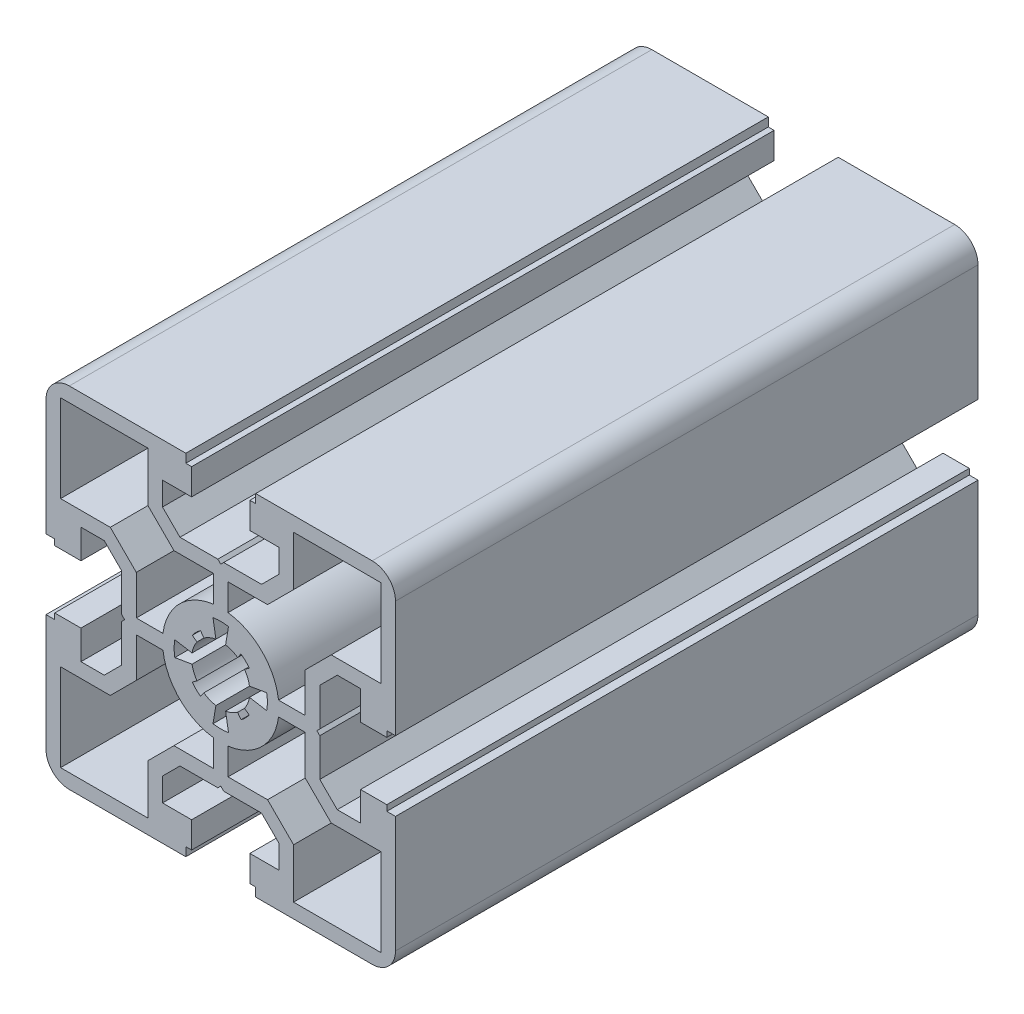
SolidWorks part; units mm, degrees
ref_plane "Ön Düzlem" through (0, 0, 0) normal (0, 0, 1) x (1, 0, 0)
ref_plane "Üst Düzlem" through (0, 0, 0) normal (0, 1, 0) x (1, 0, 0)
ref_plane "Sağ Düzlem" through (0, 0, 0) normal (1, 0, 0) x (0, 0, -1)
ref_plane "Düzlem1" through (0, 0, 100) normal (0, 0, 1) x (1, 0, 0)
sketch "Çizim1" plane through (0, 0, 100) normal (0, 0, 1) x (1, 0, 0)
  line L0 (0.833, -4.9301) -> (1.3328, -7.8882)
  line L1 (-1.3328, -7.8882) -> (-0.833, -4.9301)
  line L2 (-2.8971, -4.0751) -> (-3.4765, -4.8902)
  line L3 (-4.8902, -3.4765) -> (-4.0751, -2.8971)
  line L4 (-4.9301, -0.833) -> (-7.8882, -1.3328)
  line L5 (-7.8882, 1.3328) -> (-4.9301, 0.833)
  line L6 (-4.0751, 2.8971) -> (-4.8902, 3.4765)
  line L7 (-3.4765, 4.8902) -> (-2.8971, 4.0751)
  line L8 (-0.833, 4.9301) -> (-1.3328, 7.8882)
  line L9 (1.3328, 7.8882) -> (0.833, 4.9301)
  line L10 (2.8971, 4.0751) -> (3.4765, 4.8902)
  line L11 (4.8902, 3.4765) -> (4.0751, 2.8971)
  line L12 (4.9301, 0.833) -> (7.8882, 1.3328)
  line L13 (7.8882, -1.3328) -> (4.9301, -0.833)
  line L14 (4.0751, -2.8971) -> (4.8902, -3.4765)
  line L15 (3.4765, -4.8902) -> (2.8971, -4.0751)
  line L16 (12.5, 18.9645) -> (12.5, 27.5)
  line L17 (12.5, 27.5) -> (27.5, 27.5)
  line L18 (27.5, 27.5) -> (27.5, 12.5)
  line L19 (27.5, 12.5) -> (18.9645, 12.5)
  line L20 (18.9645, 12.5) -> (14.5, 8.0355)
  line L21 (14.5, 8.0355) -> (14.5, 1.25)
  line L22 (14.5, 1.25) -> (9.9216, 1.25)
  line L23 (1.25, 9.9216) -> (1.25, 14.5)
  line L24 (1.25, 14.5) -> (8.0355, 14.5)
  line L25 (8.0355, 14.5) -> (12.5, 18.9645)
  line L26 (18.9645, -12.5) -> (27.5, -12.5)
  line L27 (27.5, -12.5) -> (27.5, -27.5)
  line L28 (27.5, -27.5) -> (12.5, -27.5)
  line L29 (12.5, -27.5) -> (12.5, -18.9645)
  line L30 (12.5, -18.9645) -> (8.0355, -14.5)
  line L31 (8.0355, -14.5) -> (1.25, -14.5)
  line L32 (1.25, -14.5) -> (1.25, -9.9216)
  line L33 (9.9216, -1.25) -> (14.5, -1.25)
  line L34 (14.5, -1.25) -> (14.5, -8.0355)
  line L35 (14.5, -8.0355) -> (18.9645, -12.5)
  line L36 (-12.5, -18.9645) -> (-12.5, -27.5)
  line L37 (-12.5, -27.5) -> (-27.5, -27.5)
  line L38 (-27.5, -27.5) -> (-27.5, -12.5)
  line L39 (-27.5, -12.5) -> (-18.9645, -12.5)
  line L40 (-18.9645, -12.5) -> (-14.5, -8.0355)
  line L41 (-14.5, -8.0355) -> (-14.5, -1.25)
  line L42 (-14.5, -1.25) -> (-9.9216, -1.25)
  line L43 (-1.25, -9.9216) -> (-1.25, -14.5)
  line L44 (-1.25, -14.5) -> (-8.0355, -14.5)
  line L45 (-8.0355, -14.5) -> (-12.5, -18.9645)
  line L46 (-18.9645, 12.5) -> (-27.5, 12.5)
  line L47 (-27.5, 12.5) -> (-27.5, 27.5)
  line L48 (-27.5, 27.5) -> (-12.5, 27.5)
  line L49 (-12.5, 27.5) -> (-12.5, 18.9645)
  line L50 (-12.5, 18.9645) -> (-8.0355, 14.5)
  line L51 (-8.0355, 14.5) -> (-1.25, 14.5)
  line L52 (-1.25, 14.5) -> (-1.25, 9.9216)
  line L53 (-9.9216, 1.25) -> (-14.5, 1.25)
  line L54 (-14.5, 1.25) -> (-14.5, 8.0355)
  line L55 (-14.5, 8.0355) -> (-18.9645, 12.5)
  line L56 (6, -28.5) -> (6, -30)
  line L57 (6, -30) -> (26, -30)
  line L58 (30, -26) -> (30, -6)
  line L59 (30, -6) -> (28.5, -6)
  line L60 (28.5, -6) -> (28.5, -5)
  line L61 (28.5, -5) -> (24, -5)
  line L62 (24, -5) -> (24, -10)
  line L63 (24, -10) -> (20, -10)
  line L64 (20, -10) -> (17, -7)
  line L65 (17, -7) -> (17, -0.5)
  line L66 (17, -0.5) -> (16.5, 0)
  line L67 (16.5, 0) -> (17, 0.5)
  line L68 (17, 0.5) -> (17, 7)
  line L69 (17, 7) -> (20, 10)
  line L70 (20, 10) -> (24, 10)
  line L71 (24, 10) -> (24, 5)
  line L72 (24, 5) -> (28.5, 5)
  line L73 (28.5, 5) -> (28.5, 6)
  line L74 (28.5, 6) -> (30, 6)
  line L75 (30, 6) -> (30, 26)
  line L76 (26, 30) -> (6, 30)
  line L77 (6, 30) -> (6, 28.5)
  line L78 (6, 28.5) -> (5, 28.5)
  line L79 (5, 28.5) -> (5, 24)
  line L80 (5, 24) -> (10, 24)
  line L81 (10, 24) -> (10, 20)
  line L82 (10, 20) -> (7, 17)
  line L83 (7, 17) -> (0.5, 17)
  line L84 (0.5, 17) -> (0, 16.5)
  line L85 (0, 16.5) -> (-0.5, 17)
  line L86 (-0.5, 17) -> (-7, 17)
  line L87 (-7, 17) -> (-10, 20)
  line L88 (-10, 20) -> (-10, 24)
  line L89 (-10, 24) -> (-5, 24)
  line L90 (-5, 24) -> (-5, 28.5)
  line L91 (-5, 28.5) -> (-6, 28.5)
  line L92 (-6, 28.5) -> (-6, 30)
  line L93 (-6, 30) -> (-26, 30)
  line L94 (-30, 26) -> (-30, 6)
  line L95 (-30, 6) -> (-28.5, 6)
  line L96 (-28.5, 6) -> (-28.5, 5)
  line L97 (-28.5, 5) -> (-24, 5)
  line L98 (-24, 5) -> (-24, 10)
  line L99 (-24, 10) -> (-20, 10)
  line L100 (-20, 10) -> (-17, 7)
  line L101 (-17, 7) -> (-17, 0.5)
  line L102 (-17, 0.5) -> (-16.5, 0)
  line L103 (-16.5, 0) -> (-17, -0.5)
  line L104 (-17, -0.5) -> (-17, -7)
  line L105 (-17, -7) -> (-20, -10)
  line L106 (-20, -10) -> (-24, -10)
  line L107 (-24, -10) -> (-24, -5)
  line L108 (-24, -5) -> (-28.5, -5)
  line L109 (-28.5, -5) -> (-28.5, -6)
  line L110 (-28.5, -6) -> (-30, -6)
  line L111 (-30, -6) -> (-30, -26)
  line L112 (-26, -30) -> (-6, -30)
  line L113 (-6, -30) -> (-6, -28.5)
  line L114 (-6, -28.5) -> (-5, -28.5)
  line L115 (-5, -28.5) -> (-5, -24)
  line L116 (-5, -24) -> (-10, -24)
  line L117 (-10, -24) -> (-10, -20)
  line L118 (-10, -20) -> (-7, -17)
  line L119 (-7, -17) -> (-0.5, -17)
  line L120 (-0.5, -17) -> (0, -16.5)
  line L121 (0, -16.5) -> (0.5, -17)
  line L122 (0.5, -17) -> (7, -17)
  line L123 (7, -17) -> (10, -20)
  line L124 (10, -20) -> (10, -24)
  line L125 (10, -24) -> (5, -24)
  line L126 (5, -24) -> (5, -28.5)
  line L127 (5, -28.5) -> (6, -28.5)
  arc A0 (1.3328, -7.8882) -> (-1.3328, -7.8882) centre (0, 0) cw
  arc A1 (-0.833, -4.9301) -> (-2.8971, -4.0751) centre (0, 0) cw
  arc A2 (-3.4765, -4.8902) -> (-4.8902, -3.4765) centre (0, 0) cw
  arc A3 (-4.0751, -2.8971) -> (-4.9301, -0.833) centre (0, 0) cw
  arc A4 (-7.8882, -1.3328) -> (-7.8882, 1.3328) centre (0, 0) cw
  arc A5 (-4.9301, 0.833) -> (-4.0751, 2.8971) centre (0, 0) cw
  arc A6 (-4.8902, 3.4765) -> (-3.4765, 4.8902) centre (0, 0) cw
  arc A7 (-2.8971, 4.0751) -> (-0.833, 4.9301) centre (0, 0) cw
  arc A8 (-1.3328, 7.8882) -> (1.3328, 7.8882) centre (0, 0) cw
  arc A9 (0.833, 4.9301) -> (2.8971, 4.0751) centre (0, 0) cw
  arc A10 (3.4765, 4.8902) -> (4.8902, 3.4765) centre (0, 0) cw
  arc A11 (4.0751, 2.8971) -> (4.9301, 0.833) centre (0, 0) cw
  arc A12 (7.8882, 1.3328) -> (7.8882, -1.3328) centre (0, 0) cw
  arc A13 (4.9301, -0.833) -> (4.0751, -2.8971) centre (0, 0) cw
  arc A14 (4.8902, -3.4765) -> (3.4765, -4.8902) centre (0, 0) cw
  arc A15 (2.8971, -4.0751) -> (0.833, -4.9301) centre (0, 0) cw
  arc A16 (9.9216, 1.25) -> (1.25, 9.9216) centre (0, 0) ccw
  arc A17 (1.25, -9.9216) -> (9.9216, -1.25) centre (0, 0) ccw
  arc A18 (-9.9216, -1.25) -> (-1.25, -9.9216) centre (0, 0) ccw
  arc A19 (-1.25, 9.9216) -> (-9.9216, 1.25) centre (0, 0) ccw
  arc A20 (26, -30) -> (30, -26) centre (26, -26) ccw
  arc A21 (30, 26) -> (26, 30) centre (26, 26) ccw
  arc A22 (-26, 30) -> (-30, 26) centre (-26, 26) ccw
  arc A23 (-30, -26) -> (-26, -30) centre (-26, -26) ccw
extrude "Yükseklik-Ekstrüzyon1" add sketch "Çizim1" against normal blind 100
